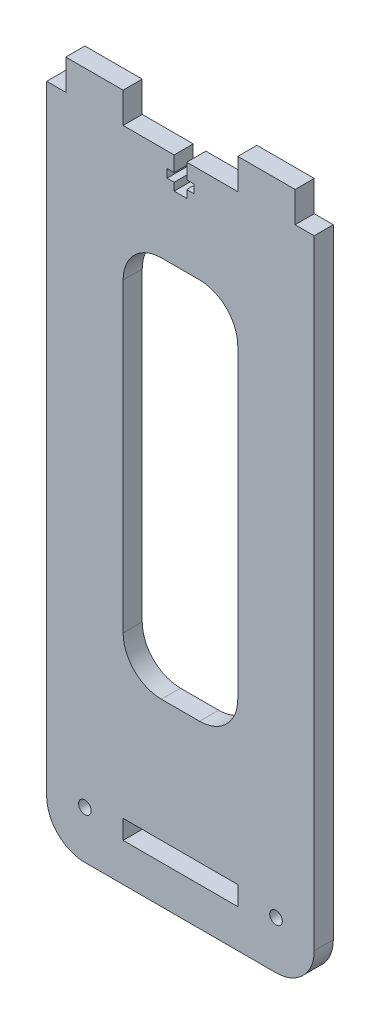
SolidWorks part; units mm, degrees
material "Acrylic (Medium-high impact)"
ref_plane "Front Plane" through (0, 0, 0) normal (0, 0, 1) x (1, 0, 0)
ref_plane "Top Plane" through (0, 0, 0) normal (0, 1, 0) x (1, 0, 0)
ref_plane "Right Plane" through (0, 0, 0) normal (1, 0, 0) x (0, 0, -1)
sketch "Sketch1" plane through (0, 0, 0) normal (0, 0, 1) x (1, 0, 0)
  line L0 (-52.5, 172) -> (-22.5, 172)
  line L1 (-72.5, 0) -> (-2.5, 0)
  line L2 (-72.5, 172) -> (-72.5, 0)
  line L3 (-72.5, 172) -> (-67.5, 172)
  line L4 (-67.5, 172) -> (-67.5, 180)
  line L5 (-67.5, 180) -> (-52.5, 180)
  line L6 (-52.5, 180) -> (-52.5, 172)
  line L7 (-37.5, 0) -> (-37.5, 47) construction
  line L8 (-22.5, 180) -> (-22.5, 172)
  line L9 (-7.5, 180) -> (-22.5, 180)
  line L10 (-7.5, 172) -> (-7.5, 180)
  line L11 (-2.5, 172) -> (-7.5, 172)
  line L13 (-22.5, 15) -> (-52.5, 15)
  line L14 (-52.5, 15) -> (-52.5, 10)
  line L15 (-52.5, 10) -> (-22.5, 10)
  line L16 (-22.5, 15) -> (-22.5, 10)
  line L18 (-32.5, 147) -> (-42.5, 147)
  line L19 (-52.5, 137) -> (-52.5, 57)
  line L22 (-2.5, 172) -> (-2.5, 0)
  line L23 (-42.5, 47) -> (-32.5, 47)
  line L24 (-22.5, 137) -> (-22.5, 57)
  arc A0 (-52.5, 57) -> (-42.5, 47) centre (-42.5, 57) ccw
  arc A1 (-22.5, 57) -> (-32.5, 47) centre (-32.5, 57) cw
  arc A2 (-22.5, 137) -> (-32.5, 147) centre (-32.5, 137) ccw
  arc A3 (-42.5, 147) -> (-52.5, 137) centre (-42.5, 137) ccw
  circle A4 centre (-62.5, 12.5) radius 1.65
  circle A5 centre (-12.5, 12.5) radius 1.65
  point P3 (-52.5, 47)
  point P13 (-37.5, 172)
  point P21 (-37.5, 10)
  point P22 (-37.5, 15)
  point P32 (-37.5, 47)
  point P33 (-37.5, 147)
  point P35 (-52.5, 147)
  dimension "D9" = 10
  dimension "D10" = 3.3
  dimension "D1" = 15
  dimension "D2" = 15
  dimension "D3" = 5
  dimension "D4" = 30
  dimension "D5" = 8
  dimension "D6" = 5
  dimension "D7" = 10
  dimension "D8" = 180
  dimension "D11" = 15
  dimension "D12" = 100
extrude "Boss-Extrude1" add sketch "Sketch1" along normal blind 5
sketch "Sketch2" plane through (0, 0, 5) normal (0, 0, 1) x (1, 0, 0)
  line L0 (-37.5, 172) -> (-37.5, 147) construction
  line L1 (-22.5, 172) -> (-52.5, 172) construction
  line L2 (-32.5, 147) -> (-42.5, 147) construction
  line L3 (-35.85, 172) -> (-35.85, 168)
  line L4 (-35.85, 168) -> (-34, 168)
  line L5 (-34, 168) -> (-34, 165.8)
  line L6 (-34, 165.8) -> (-35.85, 165.8)
  line L7 (-35.85, 165.8) -> (-35.85, 163.8)
  line L8 (-35.85, 163.8) -> (-39.15, 163.8)
  line L9 (-35.85, 172) -> (-39.15, 172)
  line L10 (-39.15, 165.8) -> (-39.15, 163.8)
  line L11 (-41, 165.8) -> (-39.15, 165.8)
  line L12 (-41, 168) -> (-41, 165.8)
  line L13 (-39.15, 168) -> (-41, 168)
  line L14 (-39.15, 172) -> (-39.15, 168)
  point P15 (-37.5, 163.8)
  dimension "D1" = 3.3
  dimension "D2" = 7
  dimension "D3" = 4
  dimension "D4" = 2.2
  dimension "D5" = 2
extrude "Cut-Extrude1" cut sketch "Sketch2" against normal through all
fillet "Fillet1" radius 10 2 edges at (-2.5, 0, 2.5) (-72.5, 0, 2.5)
